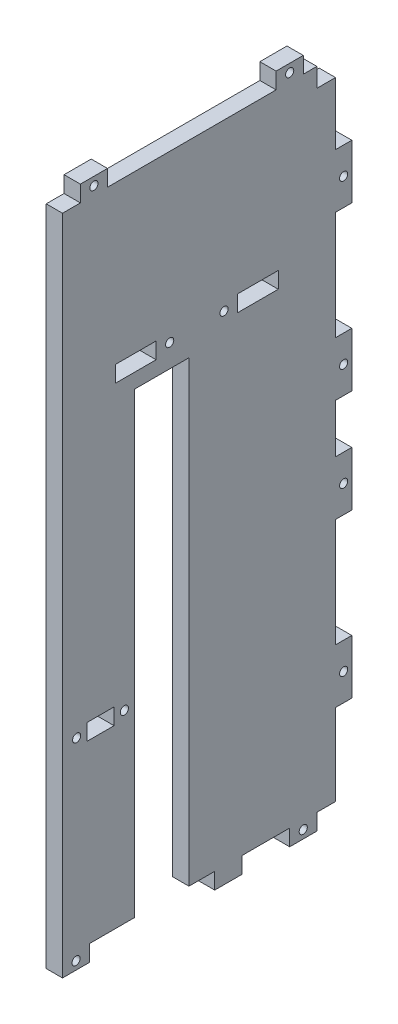
SolidWorks part; units mm, degrees
ref_plane "Plan de face" through (0, 0, 0) normal (0, 0, 1) x (1, 0, 0)
ref_plane "Plan de dessus" through (0, 0, 0) normal (0, 1, 0) x (1, 0, 0)
ref_plane "Plan de droite" through (0, 0, 0) normal (1, 0, 0) x (0, 0, -1)
sketch "Esquisse1" plane through (0, 0, 0) normal (1, 0, 0) x (0, 0, -1)
  line L0 (97.1531, 0) -> (-102.2664, 0) construction
  line L1 (-50.29, 119) -> (50.29, 119)
  line L2 (-50.29, 119) -> (-50.29, -119)
  line L3 (-50.29, -119) -> (50.29, -119)
  line L4 (50.29, 119) -> (50.29, -119)
  line L5 (0, 172.7153) -> (0, -236.1933) construction
  line L7 (-41.29, -48) -> (-31.29, -48)
  line L8 (-41.29, -48) -> (-41.29, -54)
  line L9 (-41.29, -54) -> (-31.29, -54)
  line L10 (-31.29, -48) -> (-31.29, -54)
  line L15 (-30.795, 61) -> (-15.795, 61)
  line L16 (-30.795, 61) -> (-30.795, 55)
  line L17 (-30.795, 55) -> (-15.795, 55)
  line L18 (-15.795, 61) -> (-15.795, 55)
  line L19 (14.205, 61) -> (29.205, 61)
  line L20 (14.205, 61) -> (14.205, 55)
  line L21 (14.205, 55) -> (29.205, 55)
  line L22 (29.205, 61) -> (29.205, 55)
  dimension "D1" = 238
  dimension "D2" = 100.58
  dimension "D4" = 119
  dimension "D13" = 15
  dimension "D14" = 15
  dimension "D15" = 30
  dimension "D16" = 6
  dimension "D17" = 6
  dimension "D3" = 50.29
  dimension "D5" = 58
  dimension "D6" = 19.495
  dimension "D7" = 9
  dimension "D8" = 167
  dimension "D9" = 6
  dimension "D10" = 10
extrude "Boss.-Extru.1" add sketch "Esquisse1" along normal blind 6
sketch "Esquisse3" plane through (6, 0, 0) normal (1, 0, 0) x (0, 0, -1)
  line L0 (-50.29, -119) -> (50.29, -119) construction
  line L1 (-50.29, -119) -> (-40.29, -119)
  line L2 (-50.29, -119) -> (-50.29, -125)
  line L3 (-50.29, -125) -> (-40.29, -125)
  line L4 (-40.29, -119) -> (-40.29, -125)
  line L5 (245.3741, 0) -> (-166.5298, 0) construction
  line L6 (50.29, -119) -> (50.29, 119) construction
  line L7 (33.41, -119) -> (43.41, -119)
  line L8 (33.41, -119) -> (33.41, -125)
  line L9 (33.41, -125) -> (43.41, -125)
  line L10 (0, 208.6671) -> (0, -232.3841) construction
  line L11 (-50.29, -119) -> (50.29, -119) construction
  line L12 (43.41, -119) -> (43.41, -125)
  line L13 (56.29, 29) -> (56.29, 9)
  line L14 (50.29, 9) -> (56.29, 9)
  line L15 (50.29, 29) -> (50.29, 9)
  line L16 (50.29, 29) -> (56.29, 29)
  line L17 (56.29, 89) -> (56.29, 69)
  line L18 (50.29, 69) -> (56.29, 69)
  line L19 (50.29, 89) -> (50.29, 69)
  line L20 (50.29, 89) -> (56.29, 89)
  line L21 (50.29, 119) -> (-50.29, 119) construction
  line L22 (50.29, -89) -> (56.29, -89)
  line L23 (50.29, -89) -> (50.29, -69)
  line L24 (50.29, -69) -> (56.29, -69)
  line L25 (56.29, -89) -> (56.29, -69)
  line L26 (50.29, -29) -> (56.29, -29)
  line L27 (50.29, -29) -> (50.29, -9)
  line L28 (50.29, -9) -> (56.29, -9)
  line L29 (0, -208.6671) -> (0, 232.3841) construction
  line L30 (5.79, -119) -> (15.79, -119)
  line L31 (5.79, -119) -> (5.79, -125)
  line L32 (5.79, -125) -> (15.79, -125)
  line L33 (15.79, -119) -> (15.79, -125)
  line L34 (50.29, -119) -> (50.29, 119) construction
  line L35 (56.29, -29) -> (56.29, -9)
  line L36 (38.41, 119) -> (28.41, 119)
  line L37 (38.41, 119) -> (38.41, 125)
  line L38 (38.41, 125) -> (28.41, 125)
  line L39 (28.41, 119) -> (28.41, 125)
  line L40 (-50.29, 119) -> (-50.29, -119) construction
  line L41 (-33.71, 119) -> (-43.71, 119)
  line L42 (-33.71, 119) -> (-33.71, 125)
  line L43 (-33.71, 125) -> (-43.71, 125)
  line L44 (-43.71, 119) -> (-43.71, 125)
  dimension "D2" = 10
  dimension "D3" = 6
  dimension "D4" = 10
  dimension "D5" = 6.88
  dimension "D6" = 6
  dimension "D7" = 6
  dimension "D8" = 20
  dimension "D9" = 6
  dimension "D10" = 20
  dimension "D11" = 6
  dimension "D12" = 10
  dimension "D13" = 17.62
  dimension "D14" = 30
  dimension "D15" = 40
  dimension "D16" = 6
  dimension "D17" = 10
  dimension "D18" = 11.88
  dimension "D19" = 6.58
  dimension "D20" = 10
  dimension "D21" = 6
extrude "Boss.-Extru.5" add sketch "Esquisse3" against normal blind 6
sketch "Esquisse6" plane through (6, 0, 0) normal (1, 0, 0) x (0, 0, -1)
  line L0 (-40.29, -119) -> (5.79, -119) construction
  line L1 (-23.71, -119) -> (-3.71, -119)
  line L2 (-23.71, -119) -> (-23.71, 49.59)
  line L3 (-23.71, 49.59) -> (-3.71, 49.59)
  line L4 (-3.71, -119) -> (-3.71, 49.59)
  line L5 (50.29, -69) -> (50.29, -29) construction
  line L8 (28.41, 119) -> (-33.71, 119) construction
  dimension "D1" = 20
  dimension "D2" = 69.41
  dimension "D3" = 54
extrude "Enlèv. mat.-Extru.2" cut sketch "Esquisse6" against normal blind 6
sketch "Esquisse7" plane through (0, 0, 0) normal (-1, 0, 0) x (0, 0, 1)
  line L1 (-50.29, 119) -> (-43.41, 119)
  line L2 (-50.29, 119) -> (-50.29, 112)
  line L3 (-50.29, 112) -> (-43.41, 112)
  line L4 (-43.41, 119) -> (-43.41, 112)
  dimension "D1" = 7
  dimension "D2" = 6.88
extrude "Enlèv. mat.-Extru.3" cut sketch "Esquisse7" against normal blind 6
sketch "Esquisse8" plane through (0, 0, 0) normal (-1, 0, 0) x (0, 0, 1)
  line L0 (-51.0214, 58) -> (44.3386, 58) construction
  line L1 (50.29, -125) -> (40.29, -125) construction
  line L2 (-14.205, 61) -> (-14.205, 55) construction
  line L3 (15.795, 55) -> (15.795, 61) construction
  line L5 (60.5401, -51) -> (10.4957, -51) construction
  line L6 (41.29, -48) -> (41.29, -54) construction
  line L7 (31.29, -54) -> (31.29, -48) construction
  line L8 (41.29, -54) -> (31.29, -54) construction
  line L9 (53.2872, 122) -> (-67.0711, 122) construction
  line L10 (33.71, 125) -> (43.71, 125) construction
  line L11 (-28.41, 125) -> (-28.41, 119) construction
  line L12 (33.71, 119) -> (33.71, 125) construction
  line L13 (-67.0711, -122) -> (72.8873, -122) construction
  line L16 (-33.41, -119) -> (-33.41, -125) construction
  line L17 (40.29, -125) -> (40.29, -119) construction
  line L18 (-53.29, 135.0788) -> (-53.29, -173.0788) construction
  line L19 (-56.29, 69) -> (-56.29, 89) construction
  line L21 (-56.29, -69) -> (-50.29, -69) construction
  line L22 (-50.29, 9) -> (-56.29, 9) construction
  line L23 (-56.29, 89) -> (-50.29, 89) construction
  circle A1 centre (-9.205, 58) radius 1.5
  circle A2 centre (10.795, 58) radius 1.5
  circle A4 centre (27.5, -51) radius 1.5
  circle A5 centre (45.08, -51) radius 1.5
  circle A6 centre (38.71, 122) radius 1.5
  circle A7 centre (-33.41, 122) radius 1.5
  circle A8 centre (45.29, -122) radius 1.5
  circle A9 centre (-53.29, 79) radius 1.5
  circle A10 centre (-38.41, -122) radius 1.5
  circle A11 centre (-53.29, 19) radius 1.5
  circle A12 centre (-53.29, -79) radius 1.5
  circle A13 centre (-53.29, -19) radius 1.5
  dimension "D1" = 3
  dimension "D2" = 3
  dimension "D4" = 3
  dimension "D6" = 5
  dimension "D7" = 5
  dimension "D9" = 3
  dimension "D10" = 3
  dimension "D15" = 3
  dimension "D16" = 3
  dimension "D17" = 5
  dimension "D18" = 5
  dimension "D20" = 3
  dimension "D21" = 3
  dimension "D22" = 3
  dimension "D23" = 3
  dimension "D24" = 5
  dimension "D25" = 5
  dimension "D26" = 3
  dimension "D27" = 3
  dimension "D28" = 3
  dimension "D29" = 10
  dimension "D31" = 10
  dimension "D32" = 10
  dimension "D11" = 3.79
  dimension "D12" = 3.79
  dimension "D13" = 3
  dimension "D14" = 3
  dimension "D30" = 10
extrude "Enlèv. mat.-Extru.4" cut sketch "Esquisse8" against normal blind 6
equation "\"D3@Esquisse1\"=\"D2@Esquisse1\"/2"
equation "\"D4@Esquisse1\"=\"D1@Esquisse1\"/2"
